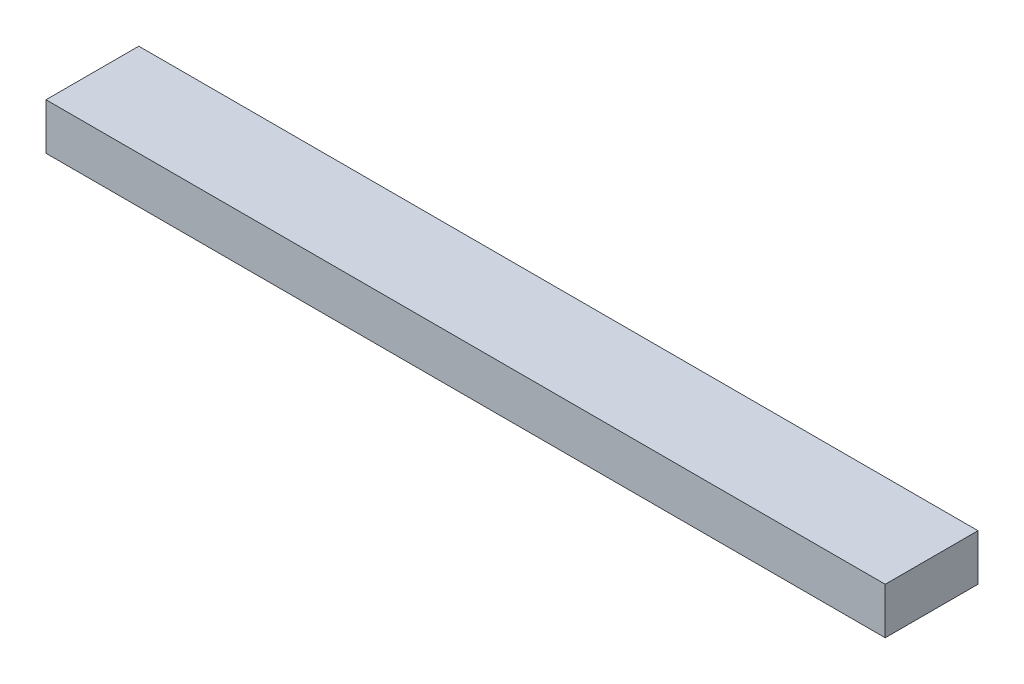
SolidWorks part; units mm, degrees
ref_plane "前视基准面" through (0, 0, 0) normal (0, 0, 1) x (1, 0, 0)
ref_plane "上视基准面" through (0, 0, 0) normal (0, 1, 0) x (1, 0, 0)
ref_plane "右视基准面" through (0, 0, 0) normal (1, 0, 0) x (0, 0, -1)
sketch "草图1" plane through (0, 0, 0) normal (1, 0, 0) x (0, 0, -1)
  line L1 (100, -50) -> (-100, -50)
  line L2 (100, -50) -> (100, 50)
  line L3 (100, 50) -> (-100, 50)
  line L4 (-100, -50) -> (-100, 50)
  line L5 (100, -50) -> (-100, 50) construction
  line L6 (100, 50) -> (-100, -50) construction
  point P0 (0, 0)
extrude "凸台-拉伸1" add sketch "草图1" against normal blind 1809
